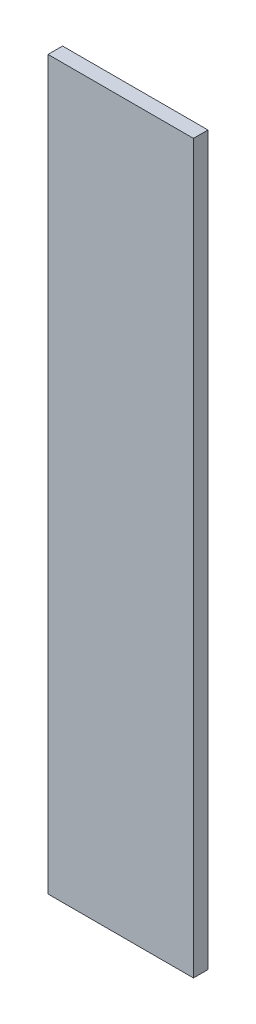
SolidWorks part; units mm, degrees
ref_plane "Front Plane" through (0, 0, 0) normal (0, 0, 1) x (1, 0, 0)
ref_plane "Top Plane" through (0, 0, 0) normal (0, 1, 0) x (1, 0, 0)
ref_plane "Right Plane" through (0, 0, 0) normal (1, 0, 0) x (0, 0, -1)
sketch "Sketch1" plane through (0, 0, 0) normal (0, 0, 1) x (1, 0, 0)
  line L1 (0, 0) -> (200, 0)
  line L2 (0, 0) -> (0, 1000)
  line L3 (0, 1000) -> (200, 1000)
  line L4 (200, 0) -> (200, 1000)
  dimension "D1" = 1000
  dimension "D2" = 200
extrude "Boss-Extrude1" add sketch "Sketch1" along normal blind 20
